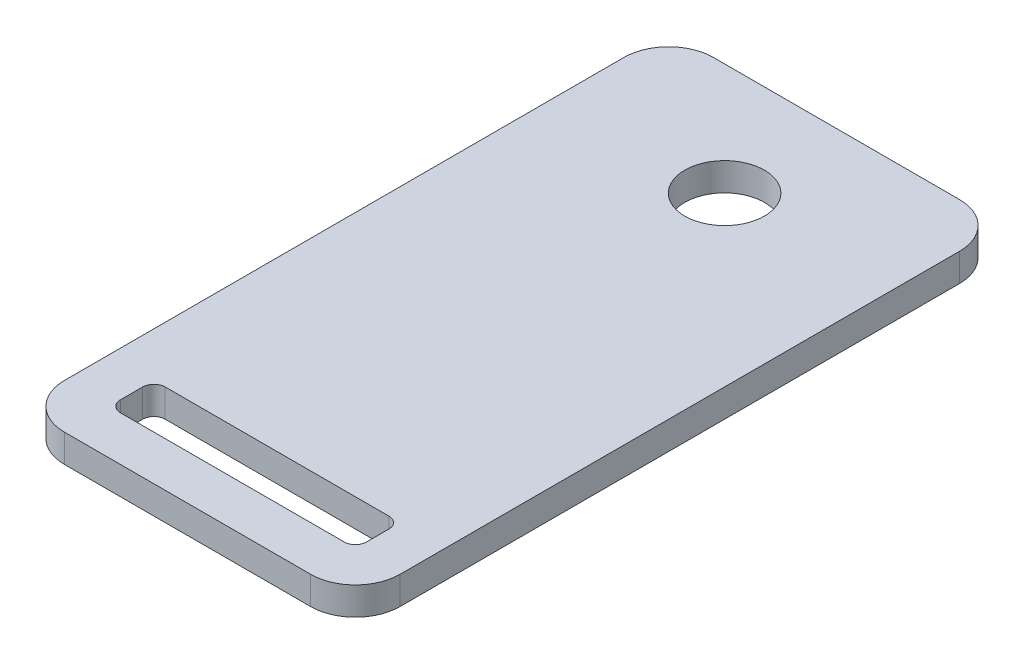
SolidWorks part; units mm, degrees
ref_plane "Front Plane" through (0, 0, 0) normal (0, 0, 1) x (1, 0, 0)
ref_plane "Top Plane" through (0, 0, 0) normal (0, 1, 0) x (1, 0, 0)
ref_plane "Right Plane" through (0, 0, 0) normal (1, 0, 0) x (0, 0, -1)
sketch "Sketch1" plane through (0, 0, 0) normal (0, 1, 0) x (1, 0, 0)
  line L1 (-19.05, 12.7) -> (19.05, 12.7)
  line L2 (-19.05, 12.7) -> (-19.05, -60.96)
  line L3 (-19.05, -60.96) -> (19.05, -60.96)
  line L4 (19.05, 12.7) -> (19.05, -60.96)
  line L5 (-13.97, -50.8) -> (13.97, -50.8)
  line L6 (-13.97, -50.8) -> (-13.97, -55.88)
  line L7 (-13.97, -55.88) -> (13.97, -55.88)
  line L8 (13.97, -50.8) -> (13.97, -55.88)
  circle A0 centre (0, 0) radius 4.5212
  point P11 (0, 12.7)
  point P12 (-11.622, -16.8479)
  dimension "D1" = 9.0424
  dimension "D2" = 5.08
  dimension "D3" = 12.7
  dimension "D4" = 5.08
  dimension "D5" = 27.94
  dimension "D6" = 5.08
  dimension "D7" = 50.8
  dimension "D8" = 5.08
extrude "Boss-Extrude1" add sketch "Sketch1" along normal blind 3.175
fillet "Fillet1" radius 5.08 4 edges at (-19.05, 1.5875, -12.7) (19.05, 1.5875, -12.7) (19.05, 1.5875, 60.96) (-19.05, 1.5875, 60.96)
fillet "Fillet2" radius 1.27 4 edges at (-13.97, 1.5875, 55.88) (13.97, 1.5875, 55.88) (13.97, 1.5875, 50.8) (-13.97, 1.5875, 50.8)
